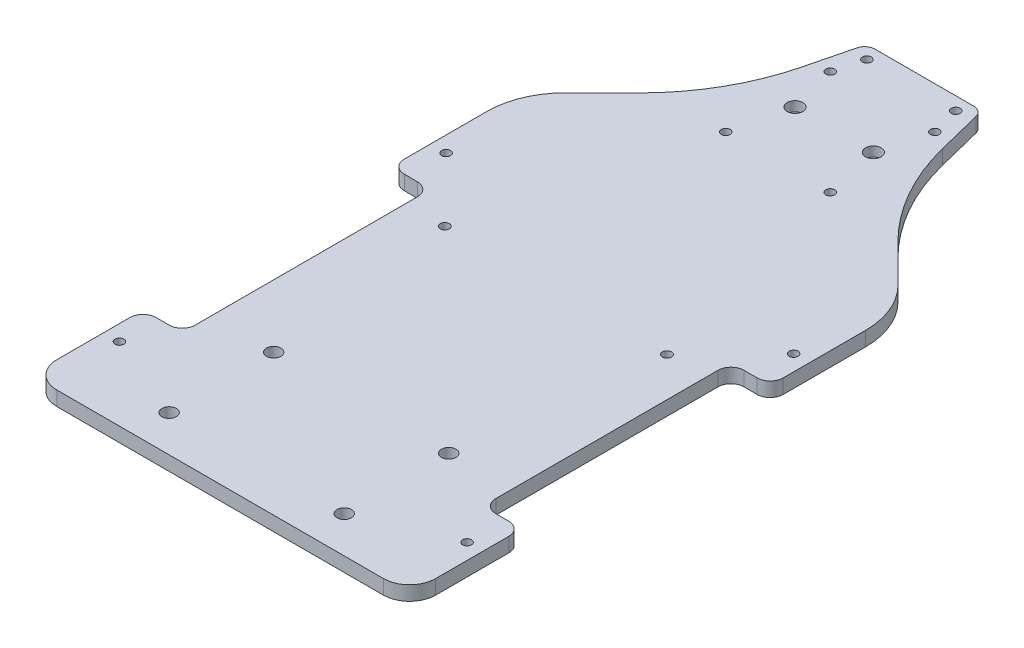
SolidWorks part; units mm, degrees
ref_plane "정면" through (0, 0, 0) normal (0, 0, 1) x (1, 0, 0)
ref_plane "윗면" through (0, 0, 0) normal (0, 1, 0) x (1, 0, 0)
ref_plane "우측면" through (0, 0, 0) normal (1, 0, 0) x (0, 0, -1)
sketch "스케치1" plane through (0, 0, 0) normal (0, 1, 0) x (1, 0, 0)
  line L0 (-857.021, 0) -> (41994.0268, 0) construction
  line L1 (0, -857.021) -> (0, 41994.0268) construction
  line L2 (-72.5, 0) -> (-72.5, -180)
  line L3 (-72.5, 95) -> (72.5, 95) construction
  line L4 (-72.5, 95) -> (-72.5, -190) construction
  line L5 (-72.5, -190) -> (-47.5, -190) construction
  line L6 (72.5, 95) -> (72.5, -190) construction
  line L7 (-62.5, -190) -> (-49.1961, -190)
  line L8 (72.5, -180) -> (72.5, 0)
  line L9 (-15.8039, -213) -> (15.8039, -213)
  line L14 (-18.846, -211.968) -> (-46.154, -191.032)
  line L15 (-22, 95) -> (22, 95)
  line L16 (-63.6708, 21.2555) -> (-49.4782, 35.3915)
  line L17 (18.846, -211.968) -> (46.154, -191.032)
  line L18 (857.021, 0) -> (-41994.0268, 0) construction
  line L23 (47.5, -190) -> (72.5, -190) construction
  line L24 (49.1961, -190) -> (62.5, -190)
  line L25 (-27, 75) -> (-22, 95)
  line L26 (63.6708, 21.2555) -> (49.4782, 35.3915)
  line L27 (27, 75) -> (22, 95)
  arc A4 (62.5, -190) -> (72.5, -180) centre (62.5, -180) ccw
  arc A5 (-62.5, -190) -> (-72.5, -180) centre (-62.5, -180) cw
  arc A12 (49.1961, -190) -> (46.154, -191.032) centre (49.1961, -195) ccw
  arc A13 (18.846, -211.968) -> (15.8039, -213) centre (15.8039, -208) cw
  arc A14 (-15.8039, -213) -> (-18.846, -211.968) centre (-15.8039, -208) cw
  arc A15 (-49.1961, -190) -> (-46.154, -191.032) centre (-49.1961, -195) cw
  arc A16 (-72.5, 0) -> (-63.6708, 21.2555) centre (-42.5, 0) cw
  arc A17 (-49.4782, 35.3915) -> (-27, 75) centre (-109.4621, 95.6155) ccw
  arc A18 (72.5, 0) -> (63.6708, 21.2555) centre (42.5, 0) ccw
  arc A19 (49.4782, 35.3915) -> (27, 75) centre (109.4621, 95.6155) cw
  point P4 (0, 0)
  point P36 (0, -213)
  point P40 (0, 95)
  point P77 (17.5, -213)
  point P80 (-17.5, -213)
  dimension "D8" = 10
  dimension "D13" = 72.5
  dimension "D14" = 5
  dimension "D17" = 20
  dimension "D15" = 30
  dimension "D16" = 85
  dimension "D1" = 145
  dimension "D2" = 285
  dimension "D3" = 190
  dimension "D9" = 35
  dimension "D10" = 23
  dimension "D11" = 25
  dimension "D12" = 44
  dimension "D18" = 5
extrude "Deck base" add sketch "스케치1" along normal blind 5.5 contours L2 A5 L7 A15 L14 A14 L9 A13 L17 A12 L24 A4 L8 A18 L26 A19 L27 L15 L25 A17 L16 A16
sketch "스케치3" plane through (0, 5.5, 0) normal (0, 1, 0) x (1, 0, 0)
  line L0 (-22, 95) -> (22, 95) construction
  line L2 (72.5, -180) -> (72.5, 0) construction
  line L3 (66.5, -146.5) -> (66.5, 0) construction
  line L4 (-200857.021, 0) -> (241994.0268, 0) construction
  line L5 (0, -3.025) -> (0, 3.025) construction
  line L6 (0, -200857.021) -> (0, 241994.0268) construction
  circle A0 centre (17, 90) radius 1.7
  circle A1 centre (66.5, -146.5) radius 1.7
  circle A2 centre (66.5, -116.5) radius 1.7
  circle A3 centre (66.5, -51.5) radius 1.7
  circle A4 centre (66.5, -21.5) radius 1.7
  circle A5 centre (-66.5, -21.5) radius 1.7
  circle A6 centre (-66.5, -51.5) radius 1.7
  circle A7 centre (-66.5, -116.5) radius 1.7
  circle A8 centre (-66.5, -146.5) radius 1.7
  circle A9 centre (-17, 90) radius 1.7
  dimension "D1" = 3.4
  dimension "D3" = 3.4
  dimension "D6" = 3.4
  dimension "D8" = 3.4
  dimension "D9" = 3.4
  dimension "D2" = 5
  dimension "D4" = 111.5
  dimension "D5" = 6
  dimension "D7" = 30
  dimension "D10" = 65
  dimension "D11" = 30
  dimension "D12" = 17
extrude "Bolt slot" cut sketch "스케치3" against normal up to next
fillet "필렛1" radius 4 2 edges at (22, 2.75, -95) (-22, 2.75, -95)
sketch "스케치11" plane through (0, 5.5, 0) normal (0, 1, 0) x (1, 0, 0)
  line L0 (-72.5, 0) -> (-72.5, -180) construction
  line L1 (-72.5, -36.5) -> (-57.5, -36.5)
  line L2 (-72.5, -36.5) -> (-72.5, -131.5)
  line L3 (-72.5, -131.5) -> (-57.5, -131.5)
  line L4 (-57.5, -36.5) -> (-57.5, -131.5)
  line L5 (0, 95) -> (0, -174.2944) construction
  line L6 (-22, 95) -> (22, 95) construction
  line L7 (0, -200857.021) -> (0, 241994.0268) construction
  line L8 (72.5, -131.5) -> (57.5, -131.5)
  line L9 (57.5, -36.5) -> (57.5, -131.5)
  line L10 (72.5, -36.5) -> (57.5, -36.5)
  line L11 (72.5, -36.5) -> (72.5, -131.5)
  circle A0 centre (-66.5, -21.5) radius 1.7 construction
  circle A1 centre (-66.5, -146.5) radius 1.7 construction
  dimension "D2" = 15
  dimension "D3" = 15
  dimension "D1" = 15
extrude "컷-돌출2" cut sketch "스케치11" against normal up to next
sketch "스케치10" plane through (0, 5.5, 0) normal (0, 1, 0) x (1, 0, 0)
  line L0 (-72.5, 0) -> (-72.5, -180) construction
  line L1 (-72.5, -174.5) -> (72.5, -174.5)
  line L2 (-72.5, -174.5) -> (-72.5, -213)
  line L3 (-72.5, -213) -> (72.5, -213)
  line L4 (72.5, -174.5) -> (72.5, -213)
  line L5 (72.5, -180) -> (72.5, 0) construction
  line L6 (-15.8039, -213) -> (15.8039, -213) construction
  circle A0 centre (-66.5, -146.5) radius 1.7 construction
  dimension "D1" = 28
extrude "컷-돌출1" cut sketch "스케치10" against normal up to next
fillet "필렛2" radius 10 2 edges at (72.5, 2.75, 174.5) (-72.5, 2.75, 174.5)
fillet "필렛3" radius 5 8 edges at (57.5, 2.75, 36.5) (72.5, 2.75, 36.5) (57.5, 2.75, 131.5) (72.5, 2.75, 131.5) (-57.5, 2.75, 131.5) (-72.5, 2.75, 131.5) (-57.5, 2.75, 36.5) (-72.5, 2.75, 36.5)
sketch "스케치4" plane through (0, 5.5, 0) normal (0, 1, 0) x (1, 0, 0)
  line L0 (-22, 95) -> (22, 95) construction
  line L1 (-20, 79) -> (20, 79) construction
  line L2 (-20, 79) -> (-20, 39) construction
  line L3 (-20, 39) -> (20, 39) construction
  line L4 (20, 79) -> (20, 39) construction
  line L5 (0, -200857.021) -> (0, 241994.0268) construction
  line L6 (0, -3.025) -> (0, 3.025) construction
  circle A0 centre (-20, 79) radius 1.7
  circle A1 centre (-20, 39) radius 1.7
  circle A2 centre (20, 39) radius 1.7
  circle A3 centre (20, 79) radius 1.7
  point P6 (0, 79)
  dimension "D4" = 3.4
  dimension "D5" = 3.4
  dimension "D1" = 40
  dimension "D2" = 40
  dimension "D3" = 16
extrude "Lidar slot" cut sketch "스케치4" against normal up to next
sketch "스케치9" plane through (0, 5.5, 0) normal (0, 1, 0) x (1, 0, 0)
  line L0 (0, -200857.021) -> (0, 241994.0268) construction
  line L1 (-24.5, 84) -> (24.5, 84) construction
  line L2 (-24.5, 84) -> (-24.5, 34) construction
  line L3 (-24.5, 34) -> (-12.5, 34) construction
  line L4 (24.5, 84) -> (24.5, 34) construction
  line L5 (-24.5, 84) -> (24.5, 34) construction
  line L6 (-24.5, 34) -> (24.5, 84) construction
  line L7 (-12.5, 29) -> (12.5, 29) construction
  line L8 (-20, 79) -> (20, 79) construction
  line L9 (12.5, 29) -> (12.5, 34) construction
  line L10 (-12.5, 29) -> (-12.5, 34) construction
  line L11 (12.5, 34) -> (24.5, 34) construction
  point P0 (0, 59)
  point P11 (0, 29)
  dimension "D1" = 49
  dimension "D2" = 50
  dimension "D3" = 5
  dimension "D4" = 25
  dimension "D5" = 5
sketch "스케치6" plane through (0, 5.5, 0) normal (0, 1, 0) x (1, 0, 0)
  line L0 (0, -200857.021) -> (0, 241994.0268) construction
  line L1 (-37, -104.5) -> (37, -104.5) construction
  line L2 (-37, -104.5) -> (-37, -174.5) construction
  line L3 (-37, -174.5) -> (37, -174.5) construction
  line L4 (37, -104.5) -> (37, -174.5) construction
  line L6 (0, -3.025) -> (0, 3.025) construction
  line L7 (-12.5, 29) -> (12.5, 29) construction
  circle A0 centre (33.5, -120.5) radius 2.75
  circle A1 centre (33.5, -160.5) radius 2.75
  circle A2 centre (-33.5, -160.5) radius 2.75
  circle A3 centre (-33.5, -120.5) radius 2.75
  point P4 (0, -104.5)
  dimension "D3" = 5.5
  dimension "D6" = 5.5
  dimension "D1" = 74
  dimension "D2" = 70
  dimension "D4" = 16
  dimension "D5" = 3.5
  dimension "D7" = 3.5
  dimension "D8" = 14
  dimension "D9" = 133.5
extrude "Vesc slot" cut sketch "스케치6" against normal up to next
sketch "스케치7" plane through (0, 5.5, 0) normal (0, 1, 0) x (1, 0, 0)
  line L0 (0, -200857.021) -> (0, 241994.0268) construction
  line L1 (-56, 12) -> (56, 12) construction
  line L2 (-56, 12) -> (-56, -104) construction
  line L3 (-56, -104) -> (56, -104) construction
  line L4 (56, 12) -> (56, -104) construction
  line L7 (12.5, 34) -> (24.5, 34) construction
  circle A4 centre (-42.5, -46) radius 1.75
  circle A5 centre (42.5, -46) radius 1.75
  point P4 (0, 12)
  dimension "D6" = 58
  dimension "D7" = 3.5
  dimension "D8" = 3.5
  dimension "D1" = 116
  dimension "D2" = 112
  dimension "D3" = 22
  dimension "D4" = 13.5
  dimension "D5" = 13.5
extrude "Nano slot" cut sketch "스케치7" against normal up to next
sketch "스케치12" plane through (0, 5.5, 0) normal (0, 1, 0) x (1, 0, 0)
  line L0 (-24.5, 34) -> (24.5, 84) construction
  line L1 (-12, 75.5) -> (12, 75.5) construction
  line L2 (-12, 75.5) -> (-12, 42.5) construction
  line L3 (-12, 42.5) -> (12, 42.5) construction
  line L4 (12, 75.5) -> (12, 42.5) construction
  line L5 (-12, 75.5) -> (12, 42.5) construction
  line L6 (-12, 42.5) -> (12, 75.5) construction
  circle A0 centre (-15, 60.5) radius 1.75
  circle A1 centre (15, 60.5) radius 1.75
  point P0 (0, 59)
  dimension "D3" = 3.5
  dimension "D4" = 3.5
  dimension "D1" = 24
  dimension "D2" = 33
  dimension "D5" = 15
  dimension "D6" = 15
  dimension "D7" = 15
extrude "컷-돌출3" cut sketch "스케치12" against normal up to next
sketch "스케치13" plane through (0, 5.5, 0) normal (0, 1, 0) x (1, 0, 0)
  circle A0 centre (-15, 60.5) radius 3
  circle A1 centre (15, 60.5) radius 3
  dimension "D1" = 6
  dimension "D2" = 6
extrude "컷-돌출4" cut sketch "스케치13" against normal blind 3.7
